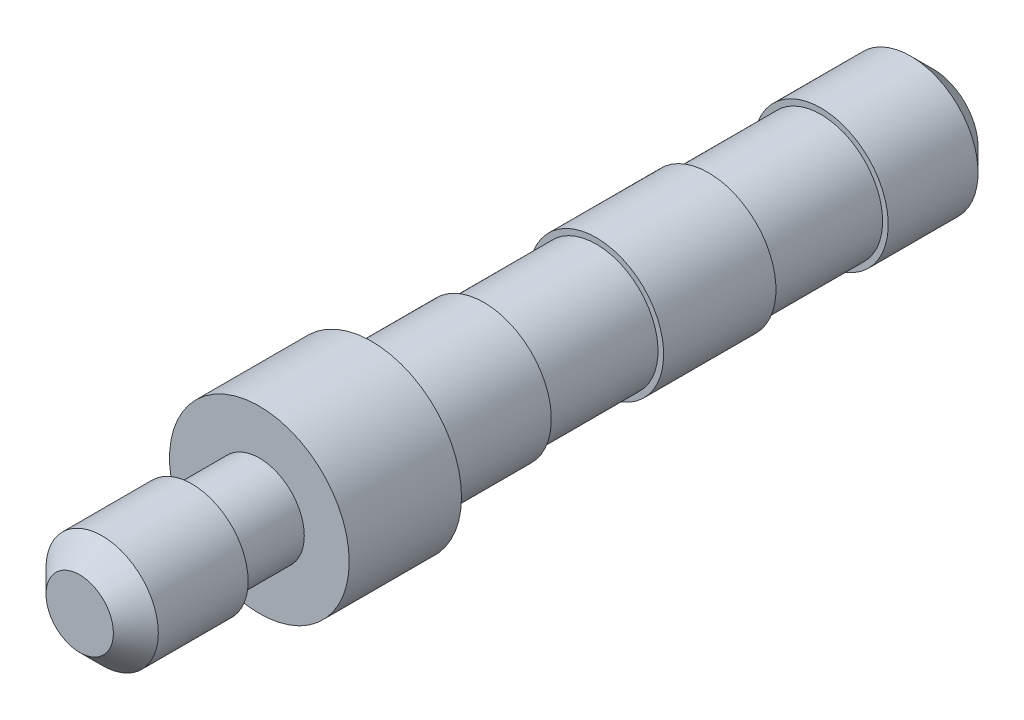
SolidWorks part; units mm, degrees
ref_plane "Plan de face" through (0, 0, 0) normal (0, 0, 1) x (1, 0, 0)
ref_plane "Plan de dessus" through (0, 0, 0) normal (0, 1, 0) x (1, 0, 0)
ref_plane "Plan de droite" through (0, 0, 0) normal (1, 0, 0) x (0, 0, -1)
sketch "Esquisse1" plane through (0, 0, 0) normal (0, 0, 1) x (1, 0, 0)
  circle A0 centre (0, 0) radius 4
  dimension "D1" = 8
extrude "Boss.-Extru.1" add sketch "Esquisse1" along normal blind 5
sketch "Esquisse5" plane through (0, 0, 0) normal (0, 0, -1) x (-1, 0, 0)
  circle A0 centre (0, 0) radius 3
  dimension "D1" = 6
extrude "Boss.-Extru.5" add sketch "Esquisse5" along normal blind 5 contours A0
sketch "Esquisse6" plane through (0, 0, -5) normal (0, 0, -1) x (-1, 0, 0)
  circle A0 centre (0, 0) radius 2.75
  dimension "D1" = 5.5
extrude "Boss.-Extru.6" add sketch "Esquisse6" along normal blind 5 contours A0
sketch "Esquisse7" plane through (0, 0, -10) normal (0, 0, -1) x (-1, 0, 0)
  circle A0 centre (0, 0) radius 3
extrude "Boss.-Extru.7" add sketch "Esquisse7" along normal blind 5
sketch "Esquisse8" plane through (0, 0, -15) normal (0, 0, -1) x (-1, 0, 0)
  circle A0 centre (0, 0) radius 2.75
  dimension "D1" = 5.5
extrude "Boss.-Extru.8" add sketch "Esquisse8" along normal blind 5
sketch "Esquisse9" plane through (0, 0, -20) normal (0, 0, -1) x (-1, 0, 0)
  circle A0 centre (0, 0) radius 3
extrude "Boss.-Extru.9" add sketch "Esquisse9" along normal blind 5
chamfer "Chanfrein1" distance 1 angle 45 1 edges at (-3, 0, -25)
sketch "Esquisse10" plane through (0, 0, 5) normal (0, 0, 1) x (1, 0, 0)
  circle A0 centre (0, 0) radius 2
  dimension "D1" = 4
extrude "Boss.-Extru.10" add sketch "Esquisse10" along normal blind 3
sketch "Esquisse11" plane through (0, 0, 8) normal (0, 0, 1) x (1, 0, 0)
  circle A0 centre (0, 0) radius 2.5
  dimension "D1" = 5
extrude "Boss.-Extru.11" add sketch "Esquisse11" along normal blind 5
chamfer "Chanfrein2" distance 1 angle 45 1 edges at (2.5, 0, 13)
